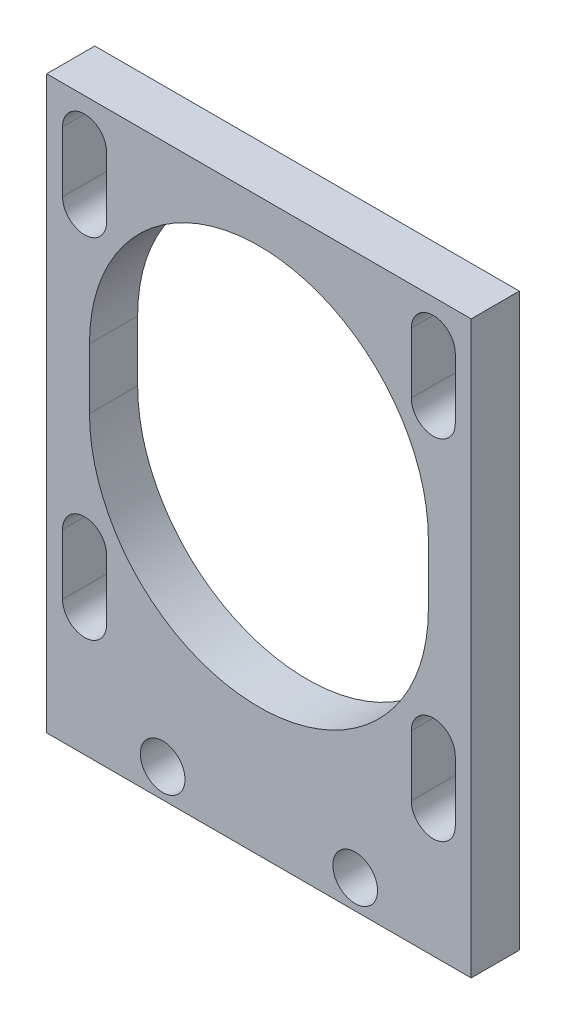
SolidWorks part; units mm, degrees
ref_plane "Front Plane" through (0, 0, 0) normal (0, 0, 1) x (1, 0, 0)
ref_plane "Top Plane" through (0, 0, 0) normal (0, 1, 0) x (1, 0, 0)
ref_plane "Right Plane" through (0, 0, 0) normal (1, 0, 0) x (0, 0, -1)
sketch "Sketch1" plane through (0, 0, 0) normal (0, 0, 1) x (1, 0, 0)
  line L1 (-14, -14) -> (14, -14)
  line L2 (-14, -14) -> (-14, 14)
  line L3 (-14, 14) -> (14, 14)
  line L4 (14, -14) -> (14, 14)
  line L5 (-14, -14) -> (14, 14) construction
  line L6 (-14, 14) -> (14, -14) construction
  point P0 (0, 0)
  dimension "D1" = 28
  dimension "D2" = 28
extrude "Boss-Extrude1" add sketch "Sketch1" along normal blind 3.175
sketch "Sketch6" plane through (0, 14, 0) normal (0, 1, 0) x (1, 0, 0)
  line L1 (-14, 0) -> (14, 0)
  line L2 (-14, 0) -> (-14, -3.175)
  line L3 (-14, -3.175) -> (14, -3.175)
  line L4 (14, 0) -> (14, -3.175)
extrude "Boss-Extrude2" add sketch "Sketch6" along normal blind 38.1
sketch "Sketch7" plane through (0, 0, 0) normal (0, 0, -1) x (-1, 0, 0)
  line L0 (-11.5, 45.6) -> (-11.5, 49.6) construction
  line L1 (-12.95, 45.6) -> (-12.95, 49.6)
  line L2 (-10.05, 45.6) -> (-10.05, 49.6)
  line L3 (-14, -14) -> (-14, 52.1) construction
  line L4 (-14, 52.1) -> (14, 52.1) construction
  line L5 (11.5, 45.6) -> (11.5, 49.6) construction
  line L6 (10.05, 45.6) -> (10.05, 49.6)
  line L7 (12.95, 45.6) -> (12.95, 49.6)
  line L8 (-11.5, 22.6) -> (-11.5, 26.6) construction
  line L9 (-12.95, 22.6) -> (-12.95, 26.6)
  line L10 (-10.05, 22.6) -> (-10.05, 26.6)
  line L11 (11.5, 22.6) -> (11.5, 26.6) construction
  line L12 (10.05, 22.6) -> (10.05, 26.6)
  line L13 (12.95, 22.6) -> (12.95, 26.6)
  line L14 (-11.5, 45.6) -> (11.5, 45.6) construction
  line L15 (-11.5, 45.6) -> (-11.5, 22.6) construction
  line L16 (0, 34.1) -> (0, 38.1) construction
  line L17 (-11.176, 34.1) -> (-11.176, 38.1)
  line L18 (11.176, 34.1) -> (11.176, 38.1)
  arc A0 (-12.95, 45.6) -> (-10.05, 45.6) centre (-11.5, 45.6) ccw
  arc A1 (-10.05, 49.6) -> (-12.95, 49.6) centre (-11.5, 49.6) ccw
  arc A2 (10.05, 45.6) -> (12.95, 45.6) centre (11.5, 45.6) ccw
  arc A3 (12.95, 49.6) -> (10.05, 49.6) centre (11.5, 49.6) ccw
  arc A4 (-12.95, 22.6) -> (-10.05, 22.6) centre (-11.5, 22.6) ccw
  arc A5 (-10.05, 26.6) -> (-12.95, 26.6) centre (-11.5, 26.6) ccw
  arc A6 (10.05, 22.6) -> (12.95, 22.6) centre (11.5, 22.6) ccw
  arc A7 (12.95, 26.6) -> (10.05, 26.6) centre (11.5, 26.6) ccw
  arc A8 (-11.176, 34.1) -> (11.176, 34.1) centre (0, 34.1) ccw
  arc A9 (11.176, 38.1) -> (-11.176, 38.1) centre (0, 38.1) ccw
  point P2 (-11.5, 47.6)
  point P13 (0, 36.1)
  point P16 (11.5, 47.6)
  point P23 (-11.5, 24.6)
  point P30 (11.5, 24.6)
  dimension "D1" = 1.45
  dimension "D9" = 11.176
  dimension "D2" = 2.5
  dimension "D3" = 2.5
  dimension "D4" = 4
  dimension "D7" = 23
  dimension "D8" = 23
  dimension "D10" = 11.5
  dimension "D6" = 2
  dimension "D5" = 2
extrude "Cut-Extrude3" cut sketch "Sketch7" against normal through all
hole_wizard "#4 Clearance Hole1" positions "Sketch9" profile "Sketch8" hole size "#4" standard "Ansi Inch"
sketch "Sketch9" plane through (0, 0, 0) normal (0, 0, -1) x (-1, 0, 0)
  point P1 (-6.35, 16.3458)
  point P4 (6.35, 16.3458)
sketch "Sketch8" plane through (6.35, 16.3458, 0) normal (1, 0, 0) x (0, 1, 0)
  line L0 (0, 0) -> (0, 13.8392)
  line L1 (0, 13.8392) -> (1.4732, 12.954)
  line L2 (1.4732, 12.954) -> (1.4732, 0)
  line L5 (1.4732, 0) -> (0, 0)
  line L10 (0, 13.8392) -> (-1.4732, 12.954) construction
  line L11 (0, -6.35) -> (0, 107.95) construction
  dimension "Hole Dia." = 2.9464
  dimension "Hole Depth" = 12.954
  dimension "Drill Angle" = 118
sketch "Sketch10" plane through (0, 0, 0) normal (0, 0, -1) x (-1, 0, 0)
  line L1 (-14, 14.448) -> (14, 14.448)
  line L2 (-14, 14.448) -> (-14, -14)
  line L3 (-14, -14) -> (14, -14)
  line L4 (14, 14.448) -> (14, -14)
  line L5 (-14, 14.448) -> (14, -14) construction
  line L6 (-14, -14) -> (14, 14.448) construction
  point P0 (0, 0.224)
  dimension "D1" = 28.448
extrude "Cut-Extrude4" cut sketch "Sketch10" against normal through all
